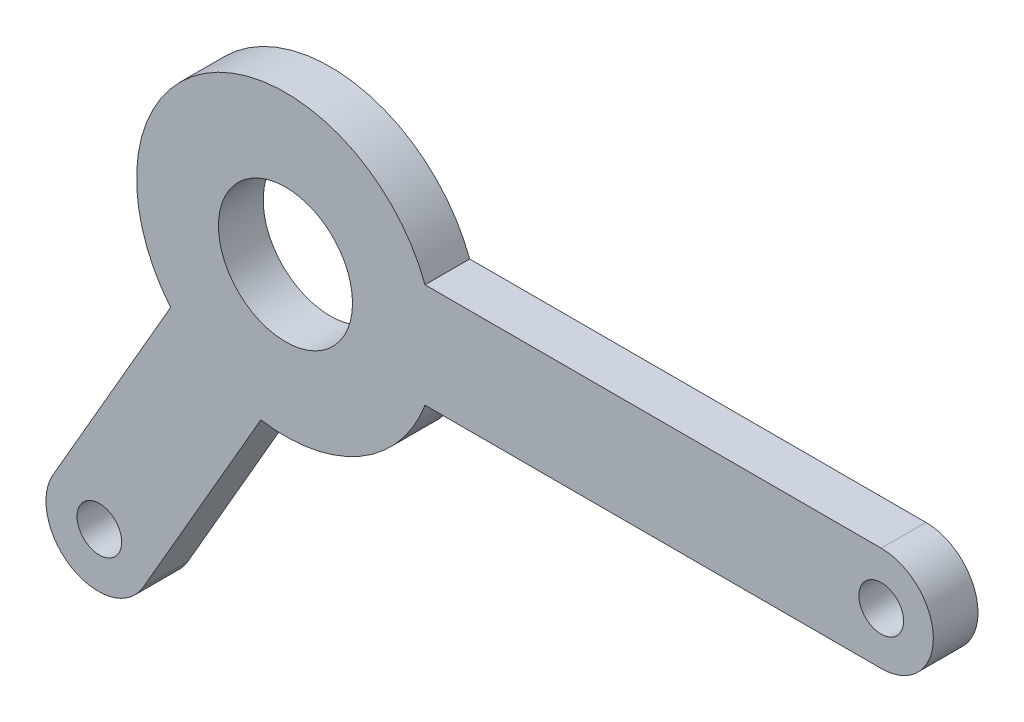
SolidWorks part; units mm, degrees
ref_plane "Front Plane" through (0, 0, 0) normal (0, 0, 1) x (1, 0, 0)
ref_plane "Top Plane" through (0, 0, 0) normal (0, 1, 0) x (1, 0, 0)
ref_plane "Right Plane" through (0, 0, 0) normal (1, 0, 0) x (0, 0, -1)
sketch "Sketch1" plane through (0, 0, 0) normal (0, 0, 1) x (1, 0, 0)
  line L0 (0, 0) -> (200, 0) construction
  line L1 (0, 0) -> (-62.5, -108.2532) construction
  line L2 (-8.2633, -49.3125) -> (-47.7712, -117.7422)
  line L3 (-38.5742, -31.8125) -> (-78.0821, -100.2422)
  line L5 (200, -17.5) -> (46.8375, -17.5)
  line L6 (46.8375, 17.5) -> (200, 17.5)
  circle A0 centre (0, 0) radius 22.5
  arc A1 (46.8375, 17.5) -> (-38.5742, -31.8125) centre (0, 0) ccw
  circle A2 centre (200, 0) radius 7.5
  arc A3 (200, 17.5) -> (200, -17.5) centre (200, 0) cw
  circle A4 centre (-62.5, -108.2532) radius 7.5
  arc A5 (-78.0821, -100.2422) -> (-47.7712, -117.7422) centre (-62.9266, -108.9922) ccw
  arc A6 (-8.2633, -49.3125) -> (46.8375, -17.5) centre (0, 0) ccw
  point P3 (0, 0)
  point P17 (0, 0)
  dimension "D1" = 45
  dimension "D2" = 100
  dimension "D5" = 120
  dimension "D7" = 15
  dimension "D8" = 35
  dimension "D3" = 200
  dimension "D4" = 125
extrude "Boss-Extrude1" add sketch "Sketch1" along normal blind 15
